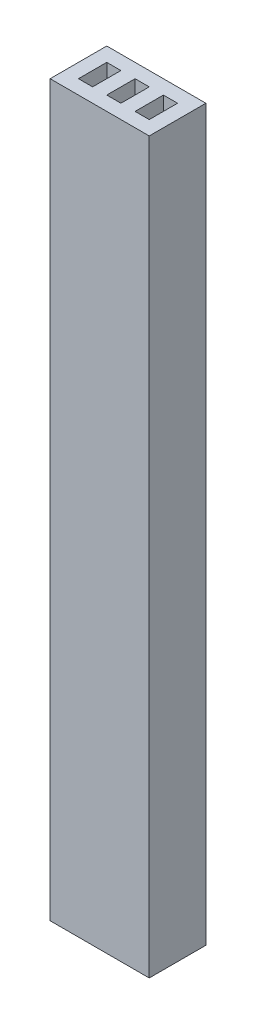
SolidWorks part; units mm, degrees
ref_plane "Front Plane" through (0, 0, 0) normal (0, 0, 1) x (1, 0, 0)
ref_plane "Top Plane" through (0, 0, 0) normal (0, 1, 0) x (1, 0, 0)
ref_plane "Right Plane" through (0, 0, 0) normal (1, 0, 0) x (0, 0, -1)
sketch "Sketch1" plane through (0, 0, 0) normal (0, 1, 0) x (1, 0, 0)
  line L0 (1, 0) -> (2, 0) construction
  line L1 (0, 0) -> (1, 0)
  line L2 (0, 0) -> (0, 2)
  line L3 (0, 2) -> (1, 2)
  line L4 (1, 0) -> (1, 2)
  line L5 (3, 0) -> (4, 0) construction
  line L6 (2, 0) -> (3, 0)
  line L7 (2, 0) -> (2, 2)
  line L8 (2, 2) -> (3, 2)
  line L9 (3, 0) -> (3, 2)
  line L10 (5, 0) -> (6, 0) construction
  line L11 (4, 0) -> (5, 0)
  line L12 (4, 0) -> (4, 2)
  line L13 (4, 2) -> (5, 2)
  line L14 (5, 0) -> (5, 2)
  line L15 (6, 0) -> (6, -1) construction
  line L16 (0, 2) -> (0, 3) construction
  line L17 (0, 3) -> (-1, 3) construction
  line L19 (-1, 3) -> (6, 3)
  line L20 (-1, 3) -> (-1, -1)
  line L21 (-1, -1) -> (6, -1)
  line L22 (6, 3) -> (6, -1)
extrude "Boss-Extrude1" add sketch "Sketch1" along normal blind 51.5
